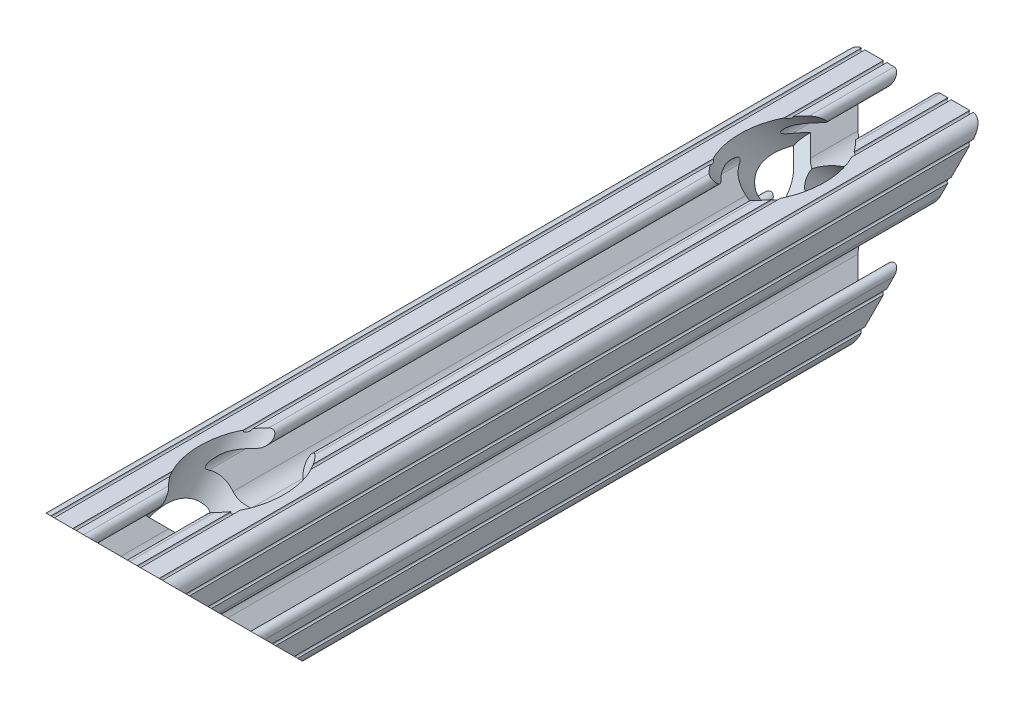
SolidWorks part; units mm, degrees
material "6063-T5"
ref_plane "Front Plane" through (0, 0, 0) normal (0, 0, 1) x (1, 0, 0)
ref_plane "Top Plane" through (0, 0, 0) normal (0, 1, 0) x (1, 0, 0)
ref_plane "Right Plane" through (0, 0, 0) normal (1, 0, 0) x (0, 0, -1)
sketch "Sketch1" plane through (0, 0, 0) normal (0, 0, 1) x (1, 0, 0)
  line L0 (0, 12.7) -> (-12.7, 12.7) construction
  line L1 (-4.5085, 0) -> (-4.5085, 2.9459)
  line L2 (-6.0545, 12.7) -> (-10.1745, 12.7) construction
  line L3 (-11.6284, 12.3843) -> (-4.3434, 12.3843) construction
  line L4 (-6.3702, 10.4902) -> (-6.3702, 12.7) construction
  line L6 (-2.9459, 4.5085) -> (0, 4.5085)
  line L7 (0, 0) -> (0, 12.7) construction
  line L8 (0, 0) -> (-12.7, 0) construction
  line L9 (0.7813, 0.7813) -> (-0.7813, -0.7813) construction
  line L10 (-2.9459, 4.5085) -> (-7.1192, 8.6818)
  line L11 (-4.5085, 2.9459) -> (-8.6818, 7.1192)
  line L13 (0, 0) -> (-12.7, 12.7) construction
  line L14 (-10.4902, 12.7) -> (-4.3434, 12.7)
  line L15 (-4.3434, 12.7) -> (-4.3434, 10.4902) construction
  line L16 (-4.3434, 10.4902) -> (-6.3702, 10.4902)
  line L17 (-12.7, 10.4902) -> (-12.7, 4.3434)
  line L18 (-10.4902, 4.3434) -> (-10.4902, 6.3702)
  circle A0 centre (0, 0) radius 2.5781
  arc A1 (-4.3434, 10.4902) -> (-4.3434, 12.7) centre (-4.3434, 11.5951) ccw
  arc A2 (-7.1192, 8.6818) -> (-6.3702, 10.4902) centre (-6.3702, 9.4309) cw
  arc A3 (-8.6818, 7.1192) -> (-10.4902, 6.3702) centre (-9.4309, 6.3702) ccw
  arc A4 (-10.4902, 4.3434) -> (-12.7, 4.3434) centre (-11.5951, 4.3434) cw
  arc A5 (-10.4902, 12.7) -> (-12.7, 10.4902) centre (-10.4902, 10.4902) ccw
  arc A6 (-10.4902, 12.7) -> (-9.8588, 12.7) centre (-10.1745, 12.7) ccw
  arc A7 (-6.3702, 12.7) -> (-5.7388, 12.7) centre (-6.0545, 12.7) ccw
  arc A8 (-12.7, 6.3702) -> (-12.7, 5.7388) centre (-12.7, 6.0545) cw
  arc A9 (-12.7, 10.4902) -> (-12.7, 9.8588) centre (-12.7, 10.1745) cw
  dimension "D1" = 5.1562
  dimension "D5" = 14.859
  dimension "D9" = 0
  dimension "D2" = 25.4
  dimension "D12" = 0.6314
  dimension "D10" = 2.2098
  dimension "D3" = 9.017
  dimension "D4" = 9.017
  dimension "D6" = 25.4
  dimension "D7" = 6.477
  dimension "D8" = 2.2098
  dimension "D11" = 12.7
sketch "Sketch3" plane through (0, 0, 0) normal (0, 0, 1) x (1, 0, 0)
  line L0 (-2.9459, 4.5085) -> (0, 4.5085) construction
  line L1 (-2.9459, 4.5085) -> (-7.1192, 8.6818) construction
  line L2 (-4.3434, 10.4902) -> (-6.3702, 10.4902) construction
  line L3 (-10.4902, 12.7) -> (-4.3434, 12.7) construction
  line L4 (-4.5085, 0) -> (-4.5085, 2.9459) construction
  line L5 (-4.5085, 2.9459) -> (-8.6818, 7.1192) construction
  line L6 (-10.4902, 4.3434) -> (-10.4902, 6.3702) construction
  line L7 (-12.7, 10.4902) -> (-12.7, 4.3434) construction
  line L8 (-1.1153, 4.5085) -> (1.1153, 4.5085)
  line L9 (-4.2404, 5.803) -> (-7.1192, 8.6818)
  line L10 (-4.3434, 10.4902) -> (-6.3702, 10.4902)
  line L11 (-9.8588, 12.7) -> (-6.3702, 12.7)
  line L12 (-4.5085, -1.1153) -> (-4.5085, 1.1153)
  line L13 (-5.803, 4.2404) -> (-8.6818, 7.1192)
  line L14 (-10.4902, 4.3434) -> (-10.4902, 6.3702)
  line L15 (-12.7, 9.8588) -> (-12.7, 6.3702)
  line L16 (-5.7388, 12.7) -> (-4.3434, 12.7)
  line L17 (-12.7, 5.7388) -> (-12.7, 4.3434)
  line L18 (0, 0) -> (0, 12.7) construction
  line L19 (0, 0) -> (-12.7, 0) construction
  line L20 (12.7, 5.7388) -> (12.7, 4.3434)
  line L21 (5.7388, 12.7) -> (4.3434, 12.7)
  line L22 (12.7, 9.8588) -> (12.7, 6.3702)
  line L23 (10.4902, 4.3434) -> (10.4902, 6.3702)
  line L24 (5.803, 4.2404) -> (8.6818, 7.1192)
  line L25 (4.5085, -1.1153) -> (4.5085, 1.1153)
  line L26 (9.8588, 12.7) -> (6.3702, 12.7)
  line L27 (4.3434, 10.4902) -> (6.3702, 10.4902)
  line L28 (4.2404, 5.803) -> (7.1192, 8.6818)
  line L29 (4.2404, -5.803) -> (7.1192, -8.6818)
  line L30 (4.3434, -10.4902) -> (6.3702, -10.4902)
  line L31 (9.8588, -12.7) -> (6.3702, -12.7)
  line L32 (5.803, -4.2404) -> (8.6818, -7.1192)
  line L33 (10.4902, -4.3434) -> (10.4902, -6.3702)
  line L34 (12.7, -9.8588) -> (12.7, -6.3702)
  line L35 (5.7388, -12.7) -> (4.3434, -12.7)
  line L36 (12.7, -5.7388) -> (12.7, -4.3434)
  line L37 (-12.7, -5.7388) -> (-12.7, -4.3434)
  line L38 (-5.7388, -12.7) -> (-4.3434, -12.7)
  line L39 (-12.7, -9.8588) -> (-12.7, -6.3702)
  line L40 (-10.4902, -4.3434) -> (-10.4902, -6.3702)
  line L41 (-5.803, -4.2404) -> (-8.6818, -7.1192)
  line L42 (-9.8588, -12.7) -> (-6.3702, -12.7)
  line L43 (-4.3434, -10.4902) -> (-6.3702, -10.4902)
  line L44 (-4.2404, -5.803) -> (-7.1192, -8.6818)
  line L45 (-1.1153, -4.5085) -> (1.1153, -4.5085)
  arc A0 (-10.4902, 12.7) -> (-9.8588, 12.7) centre (-10.1745, 12.7) ccw construction
  arc A1 (-6.3702, 10.4902) -> (-7.1192, 8.6818) centre (-6.3702, 9.4309) ccw construction
  arc A2 (-4.3434, 10.4902) -> (-4.3434, 12.7) centre (-4.3434, 11.5951) ccw construction
  arc A3 (-8.6818, 7.1192) -> (-10.4902, 6.3702) centre (-9.4309, 6.3702) ccw construction
  arc A4 (-12.7, 4.3434) -> (-10.4902, 4.3434) centre (-11.5951, 4.3434) ccw construction
  arc A5 (-6.3702, 12.7) -> (-5.7388, 12.7) centre (-6.0545, 12.7) ccw construction
  arc A6 (-10.4902, 12.7) -> (-12.7, 10.4902) centre (-10.4902, 10.4902) ccw construction
  arc A7 (-12.7, 9.8588) -> (-12.7, 10.4902) centre (-12.7, 10.1745) ccw construction
  arc A8 (-12.7, 5.7388) -> (-12.7, 6.3702) centre (-12.7, 6.0545) ccw construction
  arc A9 (-10.4902, 12.7) -> (-9.8588, 12.7) centre (-10.1745, 12.7) ccw
  arc A10 (-6.3702, 10.4902) -> (-7.1192, 8.6818) centre (-6.3702, 9.4309) ccw
  arc A11 (-4.3434, 10.4902) -> (-4.3434, 12.7) centre (-4.3434, 11.5951) ccw
  arc A12 (-8.6818, 7.1192) -> (-10.4902, 6.3702) centre (-9.4309, 6.3702) ccw
  arc A13 (-12.7, 4.3434) -> (-10.4902, 4.3434) centre (-11.5951, 4.3434) ccw
  arc A14 (-6.3702, 12.7) -> (-5.7388, 12.7) centre (-6.0545, 12.7) ccw
  arc A15 (-10.4902, 12.7) -> (-12.7, 10.4902) centre (-10.4902, 10.4902) ccw
  arc A16 (-12.7, 9.8588) -> (-12.7, 10.4902) centre (-12.7, 10.1745) ccw
  arc A17 (-12.7, 5.7388) -> (-12.7, 6.3702) centre (-12.7, 6.0545) ccw
  arc A18 (-1.1153, 4.5085) -> (-4.2404, 5.803) centre (-1.1153, 8.9281) cw
  arc A19 (4.5085, 1.1153) -> (5.803, 4.2404) centre (8.9281, 1.1153) cw
  arc A20 (1.1153, 4.5085) -> (4.2404, 5.803) centre (1.1153, 8.9281) ccw
  arc A21 (-4.5085, 1.1153) -> (-5.803, 4.2404) centre (-8.9281, 1.1153) ccw
  arc A22 (12.7, 5.7388) -> (12.7, 6.3702) centre (12.7, 6.0545) cw
  arc A23 (12.7, 9.8588) -> (12.7, 10.4902) centre (12.7, 10.1745) cw
  arc A24 (10.4902, 12.7) -> (12.7, 10.4902) centre (10.4902, 10.4902) cw
  arc A25 (6.3702, 12.7) -> (5.7388, 12.7) centre (6.0545, 12.7) cw
  arc A26 (12.7, 4.3434) -> (10.4902, 4.3434) centre (11.5951, 4.3434) cw
  arc A27 (8.6818, 7.1192) -> (10.4902, 6.3702) centre (9.4309, 6.3702) cw
  arc A28 (4.3434, 10.4902) -> (4.3434, 12.7) centre (4.3434, 11.5951) cw
  arc A29 (6.3702, 10.4902) -> (7.1192, 8.6818) centre (6.3702, 9.4309) cw
  arc A30 (10.4902, 12.7) -> (9.8588, 12.7) centre (10.1745, 12.7) cw
  arc A31 (10.4902, -12.7) -> (9.8588, -12.7) centre (10.1745, -12.7) ccw
  arc A32 (6.3702, -10.4902) -> (7.1192, -8.6818) centre (6.3702, -9.4309) ccw
  arc A33 (4.3434, -10.4902) -> (4.3434, -12.7) centre (4.3434, -11.5951) ccw
  arc A34 (8.6818, -7.1192) -> (10.4902, -6.3702) centre (9.4309, -6.3702) ccw
  arc A35 (12.7, -4.3434) -> (10.4902, -4.3434) centre (11.5951, -4.3434) ccw
  arc A36 (6.3702, -12.7) -> (5.7388, -12.7) centre (6.0545, -12.7) ccw
  arc A37 (10.4902, -12.7) -> (12.7, -10.4902) centre (10.4902, -10.4902) ccw
  arc A38 (12.7, -9.8588) -> (12.7, -10.4902) centre (12.7, -10.1745) ccw
  arc A39 (12.7, -5.7388) -> (12.7, -6.3702) centre (12.7, -6.0545) ccw
  arc A40 (-4.5085, -1.1153) -> (-5.803, -4.2404) centre (-8.9281, -1.1153) cw
  arc A41 (1.1153, -4.5085) -> (4.2404, -5.803) centre (1.1153, -8.9281) cw
  arc A42 (4.5085, -1.1153) -> (5.803, -4.2404) centre (8.9281, -1.1153) ccw
  arc A43 (-1.1153, -4.5085) -> (-4.2404, -5.803) centre (-1.1153, -8.9281) ccw
  arc A44 (-12.7, -5.7388) -> (-12.7, -6.3702) centre (-12.7, -6.0545) cw
  arc A45 (-12.7, -9.8588) -> (-12.7, -10.4902) centre (-12.7, -10.1745) cw
  arc A46 (-10.4902, -12.7) -> (-12.7, -10.4902) centre (-10.4902, -10.4902) cw
  arc A47 (-6.3702, -12.7) -> (-5.7388, -12.7) centre (-6.0545, -12.7) cw
  arc A48 (-12.7, -4.3434) -> (-10.4902, -4.3434) centre (-11.5951, -4.3434) cw
  arc A49 (-8.6818, -7.1192) -> (-10.4902, -6.3702) centre (-9.4309, -6.3702) cw
  arc A50 (-4.3434, -10.4902) -> (-4.3434, -12.7) centre (-4.3434, -11.5951) cw
  arc A51 (-6.3702, -10.4902) -> (-7.1192, -8.6818) centre (-6.3702, -9.4309) cw
  arc A52 (-10.4902, -12.7) -> (-9.8588, -12.7) centre (-10.1745, -12.7) cw
  circle A53 centre (0, 0) radius 2.5781 construction
  circle A54 centre (0, 0) radius 2.5781
  point P135 (4.5085, 0)
  dimension "D2" = 4.4196
extrude "Extrude1" add sketch "Sketch3" along normal mid plane 330.2
sketch "Sketch4" plane through (0, 0, 0) normal (1, 0, 0) x (0, 0, -1)
  line L0 (-165.1, 12.7) -> (-165.1, -12.7)
  line L1 (-165.1, -12.7) -> (-50.8, -12.7)
  line L2 (-50.8, -12.7) -> (-76.2, 12.7)
  line L3 (-76.2, 12.7) -> (-165.1, 12.7)
  line L4 (76.2, 12.7) -> (50.8, -12.7)
  line L5 (50.8, -12.7) -> (165.1, -12.7)
  line L6 (165.1, -12.7) -> (165.1, 12.7)
  line L7 (165.1, 12.7) -> (76.2, 12.7)
  line L8 (-165.1, 12.7) -> (165.1, 12.7) construction
  line L9 (0, 0) -> (0, 12.7) construction
  line L10 (-76.2, 12.7) -> (76.2, 12.7) construction
  dimension "D1" = 152.4
  dimension "D2" = 45
extrude "Cut-Extrude1" cut sketch "Sketch4" against normal mid plane 76.2
sketch "Sketch5" plane through (0, -31.75, 31.75) normal (0, -0.7071, 0.7071) x (1, 0, 0)
  circle A0 centre (0, 44.9013) radius 3.2639
  ellipse E0 centre (0, 44.9013) end of major axis (0, 41.2553) minor radius 2.5781 construction
  ellipse E1 centre (0, 44.9013) end of major axis (0, 41.2553) minor radius 2.5781 construction
  dimension "D1" = 6.5278
extrude "Cut-Extrude2" cut sketch "Sketch5" against normal blind 6.35
sketch "Sketch6" plane through (0, -27.2599, 27.2599) normal (0, -0.7071, 0.7071) x (1, 0, 0)
  circle A0 centre (0, 44.9013) radius 7.9375
  circle A1 centre (0, 44.9013) radius 3.2639 construction
  dimension "D1" = 15.875
extrude "Cut-Extrude3" cut sketch "Sketch6" against normal through all
sketch "Sketch7" plane through (0, -31.75, -31.75) normal (0, -0.7071, -0.7071) x (1, 0, 0)
  circle A0 centre (0, -44.9013) radius 3.2639
  ellipse E0 centre (0, -44.9013) end of major axis (0, -48.5473) minor radius 2.5781 construction
  ellipse E1 centre (0, -44.9013) end of major axis (0, -48.5473) minor radius 2.5781 construction
  dimension "D1" = 6.5278
extrude "Cut-Extrude4" cut sketch "Sketch7" against normal blind 6.35
sketch "Sketch8" plane through (0, -27.2599, -27.2599) normal (0, -0.7071, -0.7071) x (1, 0, 0)
  circle A0 centre (0, -44.9013) radius 7.9375
  circle A1 centre (0, -44.9013) radius 3.2639 construction
  dimension "D1" = 15.875
extrude "Cut-Extrude5" cut sketch "Sketch8" against normal through all
equation "\"D10@Sketch1\" = \"D8@Sketch1\""
equation "\"D11@Sketch1\" = \"D6@Sketch1\"/2"
equation "\"D12@Sketch1\" = \"D8@Sketch1\"/3.5"
equation "\"D2@Sketch3\" = \"D8@Sketch1\"*2"
equation "\"D1@Sketch7\"=\"D1@Sketch5\""
equation "\"D1@Sketch8\" =\"D1@Sketch6\""
